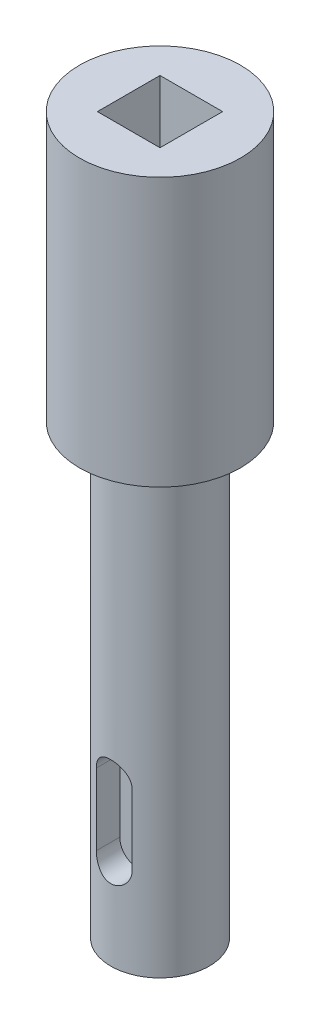
SolidWorks part; units mm, degrees
material "普通碳钢"
ref_plane "前视基准面" through (0, 0, 0) normal (0, 0, 1) x (1, 0, 0)
ref_plane "上视基准面" through (0, 0, 0) normal (0, 1, 0) x (1, 0, 0)
ref_plane "右视基准面" through (0, 0, 0) normal (1, 0, 0) x (0, 0, -1)
sketch "草图1" plane through (0, 0, 0) normal (0, 0, 1) x (1, 0, 0)
  line L0 (0, 0) -> (0, 79.5854) construction
  line L1 (0, 0) -> (-5.5, 0)
  line L2 (-5.5, 0) -> (-5.5, 50)
  line L3 (0, 80) -> (-9, 80)
  line L4 (0, 80) -> (0, 0)
  line L5 (-5.5, 50) -> (-9, 50)
  line L6 (-9, 50) -> (-9, 80)
  dimension "D1" = 80
  dimension "D2" = 5.5
  dimension "D3" = 9
  dimension "D4" = 30
revolve "旋转1" add sketch "草图1" angle 360 about L0
sketch "草图2" plane through (0, 80, 0) normal (0, 1, 0) x (1, 0, 0)
  line L1 (-3.5, -3.5) -> (3.5, -3.5)
  line L2 (-3.5, -3.5) -> (-3.5, 3.5)
  line L3 (-3.5, 3.5) -> (3.5, 3.5)
  line L4 (3.5, -3.5) -> (3.5, 3.5)
  line L5 (-3.5, -3.5) -> (3.5, 3.5) construction
  line L6 (-3.5, 3.5) -> (3.5, -3.5) construction
  point P0 (0, 0)
  dimension "D1" = 7
ref_plane "基准面1" through (0, 0, 5.5) normal (0, 0, 1) x (1, 0, 0)
extrude "切除-拉伸1" cut sketch "草图2" against normal blind 20
sketch "草图4" plane through (0, 0, 5.5) normal (0, 0, 1) x (1, 0, 0)
  line L0 (0, 10) -> (0, 18) construction
  line L1 (-2, 10) -> (-2, 18)
  line L2 (2, 10) -> (2, 18)
  arc A0 (-2, 10) -> (2, 10) centre (0, 10) ccw
  arc A1 (2, 18) -> (-2, 18) centre (0, 18) ccw
  point P3 (0, 14)
  dimension "D1" = 2
  dimension "D2" = 8
  dimension "D3" = 10
extrude "切除-拉伸2" cut sketch "草图4" against normal blind 3
equation "\"2。5\"=4.69247"
